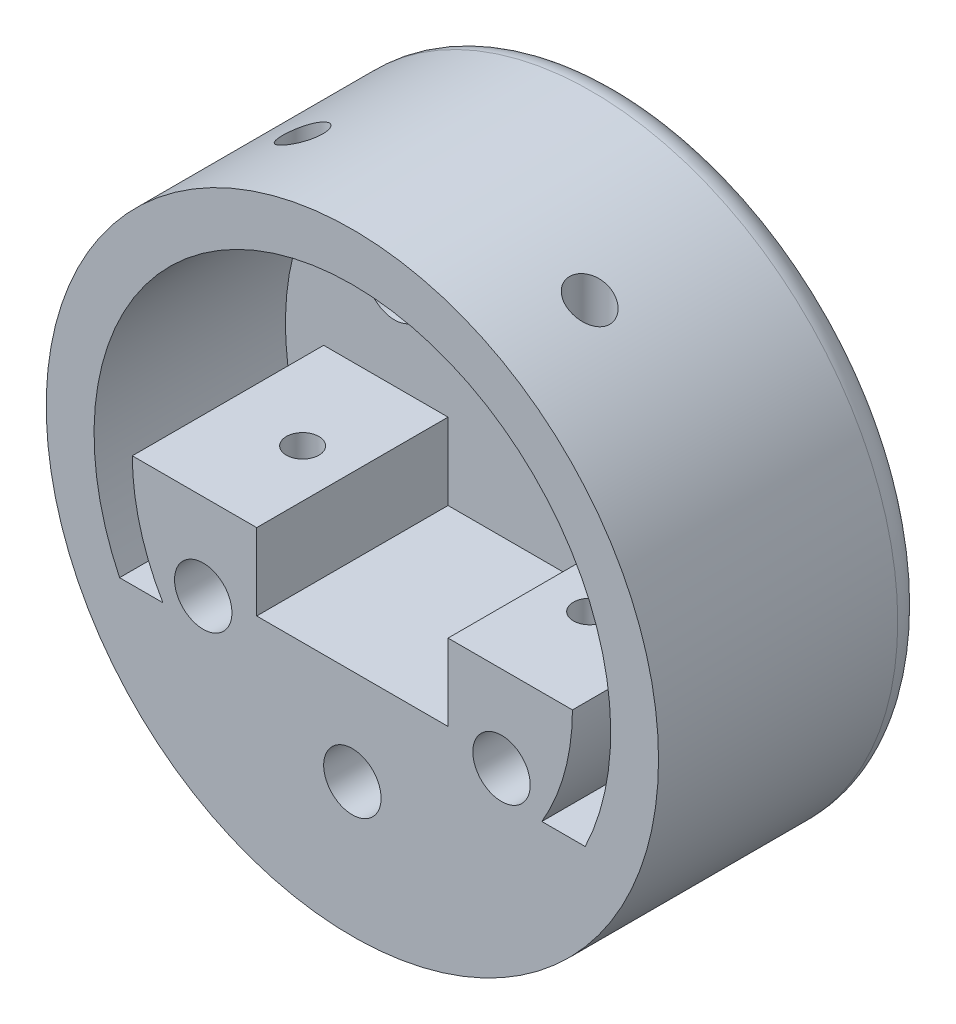
SolidWorks part; units mm, degrees
ref_plane "前视基准面" through (0, 0, 0) normal (0, 0, 1) x (1, 0, 0)
ref_plane "上视基准面" through (0, 0, 0) normal (0, 1, 0) x (1, 0, 0)
ref_plane "右视基准面" through (0, 0, 0) normal (1, 0, 0) x (0, 0, -1)
sketch "草图1" plane through (0, 0, 0) normal (0, 0, 1) x (1, 0, 0)
  circle A0 centre (0, 0) radius 50
extrude "凸台-拉伸1" add sketch "草图1" along normal blind 42
sketch "草图2" plane through (0, 0, 0) normal (0, 0, -1) x (-1, 0, 0)
  circle A0 centre (0, 0) radius 47.45
  dimension "D1" = 94.9
extrude "切除-拉伸1" cut sketch "草图2" against normal blind 9
sketch "草图3" plane through (0, 0, 9) normal (0, 0, -1) x (-1, 0, 0)
  circle A0 centre (0, 0) radius 43
  dimension "D1" = 86
extrude "切除-拉伸2" cut sketch "草图3" against normal blind 5
sketch "草图4" plane through (0, 0, 14) normal (0, 0, -1) x (-1, 0, 0)
  circle A0 centre (0, 0) radius 18 construction
  circle A1 centre (0, -18) radius 1.7
  circle A2 centre (-15.5885, -9) radius 1.7
  circle A3 centre (-15.5885, 9) radius 1.7
  circle A4 centre (0, 18) radius 1.7
  circle A5 centre (15.5885, 9) radius 1.7
  circle A6 centre (15.5885, -9) radius 1.7
  point P17 (0, 0)
  dimension "D1" = 6
extrude "切除-拉伸3" cut sketch "草图4" against normal blind 49
sketch "草图5" plane through (0, 0, 42) normal (0, 0, 1) x (1, 0, 0)
  line L9 (-23, 0) -> (-10, 0)
  line L10 (23, 0) -> (10, 0)
  line L11 (-10, 0) -> (-10, -8)
  line L12 (10, 0) -> (10, -8)
  line L13 (10, -8) -> (-10, -8)
  line L14 (0, 0) -> (0, -11.7) construction
  line L15 (-19.8018, -11.7) -> (-24.3333, -11.7)
  line L16 (19.8018, -11.7) -> (24.3333, -11.7)
  circle A1 centre (0, 0) radius 52
  arc A3 (24.3333, -11.7) -> (-24.3333, -11.7) centre (0, 0) ccw
  circle A4 centre (0, 0) radius 23
  circle A5 centre (0, 0) radius 52
  circle A6 centre (0, 0) radius 32
  circle M9 centre (-15.5885, 9) radius 1.7
  circle M10 centre (0, 18) radius 1.7
  circle M11 centre (15.5885, 9) radius 1.7
  circle M13 centre (0, 0) radius 50
extrude "切除-拉伸4" cut sketch "草图5" against normal blind 20 contours A6 M13 | A3 A4 | L10 A4 L9 L11 L13 L12 M10 M11 M9 | A1
fillet "圆角1" radius 2 1 edges at (50, 0, 22)
fillet "圆角2" radius 2 1 edges at (32, 0, 22)
sketch "草图6" plane through (0, 0, 0) normal (0, 1, 0) x (1, 0, 0)
  line L0 (0, -42) -> (0, -32.2) construction
  line L1 (-32, -42) -> (32, -42) construction
  line L2 (0, -32.2) -> (-15, -32.2) construction
  line L3 (0, -32.2) -> (15, -32.2) construction
  circle A0 centre (-15, -32.2) radius 1.7
  circle A1 centre (15, -32.2) radius 1.7
extrude "切除-拉伸5" cut sketch "草图6" against normal through all both and the other way through all
sketch "草图7" plane through (0, 0, 42) normal (0, 0, 1) x (1, 0, 0)
  circle A0 centre (-15.5885, -9) radius 3
  circle A1 centre (0, -18) radius 3
  circle A2 centre (15.5885, -9) radius 3
extrude "切除-拉伸6" cut sketch "草图7" against normal blind 17.5
ref_plane "基准面1" through (0, -23, 0) normal (0, 1, 0) x (1, 0, 0)
sketch "草图8" plane through (0, -23, 0) normal (0, 1, 0) x (1, 0, 0)
  circle A0 centre (-15, -32.2) radius 3
  circle A1 centre (15, -32.2) radius 3
extrude "切除-拉伸7" cut sketch "草图8" against normal blind 8
ref_plane "基准面2" through (0, 25, 0) normal (0, 1, 0) x (1, 0, 0)
sketch "草图9" plane through (0, 25, 0) normal (0, 1, 0) x (1, 0, 0)
  line L0 (15, -32.2) -> (0, -32.2) construction
  line L1 (0, -32.2) -> (0, -42) construction
  line L3 (-32, -42) -> (32, -42) construction
  circle A0 centre (-15, -32.2) radius 2.1
  circle A1 centre (15, -32.2) radius 2.1
extrude "切除-拉伸8" cut sketch "草图9" against normal mid plane 10
sketch "草图10" plane through (0, 0, 22) normal (0, 0, 1) x (1, 0, 0)
  circle A0 centre (-15.5885, 9) radius 3
  circle A1 centre (0, 18) radius 3
  circle A2 centre (15.5885, 9) radius 3
extrude "切除-拉伸9" cut sketch "草图10" against normal blind 2.5
sketch "草图11" plane through (0, 0, 42) normal (0, 0, 1) x (1, 0, 0)
  circle A0 centre (0, 0) radius 32
  circle A1 centre (0, 0) radius 50
extrude "切除-拉伸10" cut sketch "草图11" against normal through all
fillet "圆角3" radius 3 1 edges at (-32, 0, 14)
